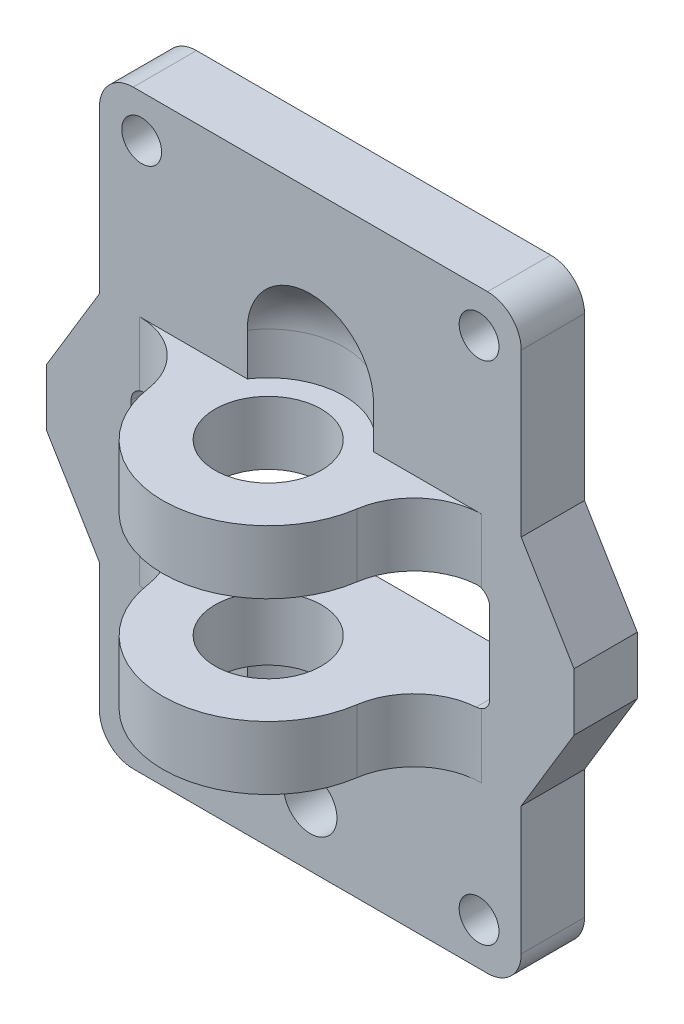
SolidWorks part; units mm, degrees
ref_plane "Front Plane" through (0, 0, 0) normal (0, 0, 1) x (1, 0, 0)
ref_plane "Top Plane" through (0, 0, 0) normal (0, 1, 0) x (1, 0, 0)
ref_plane "Right Plane" through (0, 0, 0) normal (1, 0, 0) x (0, 0, -1)
sketch "Sketch1" plane through (0, 0, 0) normal (0, 0, 1) x (1, 0, 0)
  line L1 (-15.875, -22.225) -> (15.875, -22.225)
  line L2 (-15.875, -22.225) -> (-15.875, 22.225)
  line L3 (-15.875, 22.225) -> (15.875, 22.225)
  line L4 (15.875, -22.225) -> (15.875, 22.225)
  line L5 (-15.875, -22.225) -> (15.875, 22.225) construction
  line L6 (-15.875, 22.225) -> (15.875, -22.225) construction
  point P0 (0, 0)
  dimension "D1" = 44.45
  dimension "D2" = 31.75
extrude "Boss-Extrude1" add sketch "Sketch1" along normal blind 4.7625
sketch "Sketch2" plane through (0, 0, 4.7625) normal (0, 0, 1) x (1, 0, 0)
  line L0 (0, 22.225) -> (0, -22.225) construction
  line L1 (-15.875, 22.225) -> (-12.7, 22.225) construction
  line L2 (-15.875, 22.225) -> (-15.875, 19.05) construction
  line L3 (-15.875, 19.05) -> (-12.7, 19.05) construction
  line L4 (-12.7, 22.225) -> (-12.7, 19.05) construction
  line L5 (15.875, 22.225) -> (-15.875, 22.225) construction
  line L6 (-15.875, -22.225) -> (15.875, -22.225) construction
  line L7 (0, -17.78) -> (0, -22.225) construction
  line L8 (-15.875, 0) -> (15.875, 0) construction
  line L9 (-15.875, 22.225) -> (-15.875, -22.225) construction
  line L10 (15.875, -22.225) -> (15.875, 22.225) construction
  circle A0 centre (-12.7, 19.05) radius 1.5
  circle A1 centre (12.7, 19.05) radius 1.5
  circle A2 centre (0, -17.78) radius 2
  circle A3 centre (12.7, -19.05) radius 1.5
  circle A4 centre (-12.7, -19.05) radius 1.5
  dimension "D1" = 3
  dimension "D2" = 4
  dimension "D3" = 3.175
  dimension "D4" = 4.445
extrude "Cut-Extrude1" cut sketch "Sketch2" against normal through all
fillet "Fillet1" radius 2.54 4 edges at (-15.875, -22.225, 2.3813) (-15.875, 22.225, 2.3813) (15.875, -22.225, 2.3813) (15.875, 22.225, 2.3813)
sketch "Sketch3" plane through (0, 0, 4.7625) normal (0, 0, 1) x (1, 0, 0)
  line L0 (0, -17.78) -> (0, -5.27) construction
  line L1 (-13.5, -5.27) -> (13.5, -5.27)
  line L2 (-13.5, -5.27) -> (-13.5, 2.73)
  line L3 (-13.5, 2.73) -> (13.5, 2.73)
  line L4 (13.5, -5.27) -> (13.5, 2.73)
  line L5 (-13.5, -5.27) -> (13.5, 2.73) construction
  line L6 (-13.5, 2.73) -> (13.5, -5.27) construction
  point P0 (0, -1.27)
  dimension "D1" = 8
  dimension "D2" = 27
  dimension "D3" = 16.51
extrude "Cut-Extrude2" cut sketch "Sketch3" against normal through all
fillet "Fillet2" radius 1 4 edges at (13.5, 2.73, 2.3813) (-13.5, 2.73, 2.3813) (-13.5, -5.27, 2.3813) (13.5, -5.27, 2.3813)
sketch "Sketch4" plane through (0, 2.73, 0) normal (0, -1, 0) x (1, 0, 0)
  line L1 (0, 0) -> (0, 7.9375) construction
  line L2 (12.5, 0) -> (-12.5, 0) construction
  circle A0 centre (0, 7.9375) radius 11 construction
  circle A1 centre (0, 7.9375) radius 7.9375
  circle A2 centre (0, 7.9375) radius 4
  dimension "D1" = 22
  dimension "D2" = 15.875
  dimension "D3" = 8
extrude "Boss-Extrude2" add sketch "Sketch4" against normal blind 4.7625
sketch "Sketch5" plane through (0, 2.73, 0) normal (0, -1, 0) x (1, 0, 0)
  circle A0 centre (0, 7.9375) radius 4
extrude "Cut-Extrude3" cut sketch "Sketch5" against normal up to surface (4.7625 mm away) up to face at (0, 7.4925, 9.3344)
sketch "Sketch6" plane through (0, 7.4925, 0) normal (0, -1, 0) x (1, 0, 0)
  circle A0 centre (0, 7.9375) radius 5.715
  dimension "D1" = 11.43
extrude "Cut-Extrude4" cut sketch "Sketch6" against normal blind 3.175
sketch "Sketch7" plane through (0, 10.6675, 0) normal (0, -1, 0) x (1, 0, 0)
  line L0 (5.715, 7.9375) -> (-5.715, 7.9375)
  arc A0 (-5.715, 7.9375) -> (5.715, 7.9375) centre (0, 7.9375) ccw
  arc A1 (-4.7519, 4.7625) -> (4.7519, 4.7625) centre (0, 7.9375) ccw construction
revolve "Cut-Revolve1" cut sketch "Sketch7" angle 90 about L0
fillet "Fillet3" radius 5.08 2 edges at (7.2748, 5.1112, 4.7625) (-7.2748, 5.1112, 4.7625)
ref_plane "Plane1" through (0, -1.27, 0) normal (0, -1, 0) x (-1, 0, 0)
mirror "Mirror1" about plane through (0, -1.27, 0) normal (0, -1, 0) of "Fillet3", "Boss-Extrude2", "Cut-Extrude3", "Cut-Extrude4"
sketch "Sketch9" plane through (0, 0, 4.7625) normal (0, 0, 1) x (1, 0, 0)
  line L0 (-15.875, 7.4925) -> (-19.85, 0.8972)
  line L1 (-15.875, 19.685) -> (-15.875, -19.685) construction
  line L2 (-19.85, 0.8972) -> (-19.85, -3.4372)
  line L3 (-19.85, -3.4372) -> (-15.875, -10.0325)
  line L4 (-15.875, -10.0325) -> (-15.875, 7.4925)
  line L5 (-13.5, -1.27) -> (13.4365, -1.27) construction
  line L6 (-13.5, 1.73) -> (-13.5, -4.27) construction
  line L7 (-8.7312, -1.27) -> (8.7312, -1.27) construction
  line L8 (-12.5, 2.73) -> (-7.852, 2.73) construction
  dimension "D1" = 4.7625
  dimension "D2" = 6.35
extrude "Boss-Extrude3" add sketch "Sketch9" against normal up to surface (4.7625 mm away) up to face at (0, -1.27, 0)
mirror "Mirror2" about plane through (0, 0, 0) normal (1, 0, 0) of "Boss-Extrude3"
